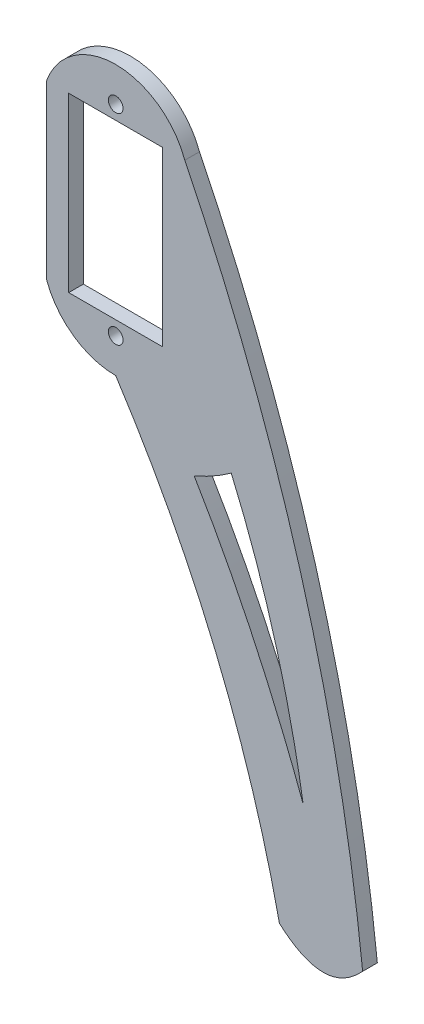
SolidWorks part; units mm, degrees
ref_plane "Front Plane" through (0, 0, 0) normal (0, 0, 1) x (1, 0, 0)
ref_plane "Top Plane" through (0, 0, 0) normal (0, 1, 0) x (1, 0, 0)
ref_plane "Right Plane" through (0, 0, 0) normal (1, 0, 0) x (0, 0, -1)
sketch "Sketch1" plane through (0, 0, 0) normal (0, 0, 1) x (1, 0, 0)
  line L0 (0, 11.75) -> (0, -11.75) construction
  line L1 (6.4, -11.75) -> (-6.4, -11.75)
  line L2 (6.4, -11.75) -> (6.4, 11.75)
  line L3 (6.4, 11.75) -> (-6.4, 11.75)
  line L4 (-6.4, -11.75) -> (-6.4, 11.75)
  line L5 (6.4, -11.75) -> (-6.4, 11.75) construction
  line L6 (6.4, 11.75) -> (-6.4, -11.75) construction
  line L9 (9.4, 11.75) -> (9.4, -11.75) construction
  line L10 (-9.4, 11.75) -> (-9.4, -11.75) construction
  line L11 (-6.4, -11.75) -> (6.4, -11.75)
  line L12 (-6.4, -11.75) -> (-6.4, -16.45) construction
  line L13 (6.4, -11.75) -> (6.4, -16.45) construction
  line L14 (-6.4, -16.45) -> (6.4, -16.45) construction
  line L15 (-38.4786, 0) -> (38.4786, 0) construction
  line L16 (-6.4, 16.45) -> (6.4, 16.45) construction
  line L17 (6.4, 11.75) -> (6.4, 16.45) construction
  line L18 (-6.4, 11.75) -> (-6.4, 16.45) construction
  line L19 (-9.4, -11.75) -> (-9.4, 11.75)
  line L20 (9.4, -11.75) -> (9.4, 11.75)
  line L21 (33.608, -71.75) -> (28.5034, -77.3391) construction
  line L22 (28.5034, -77.3391) -> (22.2808, -71.75) construction
  line L23 (15.7257, -21.9692) -> (22.5216, -37.7122) construction
  line L24 (22.5216, -37.7122) -> (25.5114, -56.0772) construction
  line L25 (10.6799, -24.817) -> (19.0882, -38.8473) construction
  line L26 (19.0882, -38.8473) -> (25.5114, -56.0772) construction
  arc A2 (9.4, 11.75) -> (-9.4, 11.75) centre (0, 11.75) ccw construction
  arc A3 (-9.4, -11.75) -> (9.4, -11.75) centre (0, -11.75) ccw construction
  circle A4 centre (0, -13.65) radius 1
  circle A5 centre (0, 13.65) radius 1
  arc A6 (-9.4, 11.75) -> (9.4, 11.75) centre (0, 8.3383) cw
  arc A7 (-9.4, -11.75) -> (9.4, -11.75) centre (0, -8.3383) ccw
  arc A8 (9.4, 11.75) -> (33.608, -71.75) centre (-214.9512, -98.5521) cw
  arc A9 (0, -18.3383) -> (22.2808, -71.75) centre (-134.0915, -105.6278) cw
  arc A10 (10.6799, -24.817) -> (15.7257, -21.9692) centre (0, 0) ccw
  spline S0 degree 2 poles (33.608, -71.75) (28.5034, -77.3391) (22.2808, -71.75) knots 0 0 0 1 1 1
  spline S1 degree 2 poles (15.7257, -21.9692) (22.5216, -37.7122) (25.5114, -56.0772) knots 0 0 0 1 1 1
  spline S2 degree 2 poles (10.6799, -24.817) (19.0882, -38.8473) (25.5114, -56.0772) knots 0 0 0 1 1 1
  point P0 (0, 0)
  point P8 (0, 0)
  point P18 (0, 0)
  point P20 (0, -16.45)
  dimension "D4" = 2
  dimension "D7" = 10
  dimension "D9" = 250
  dimension "D10" = 160
  dimension "D15" = 27.0175
  dimension "D1" = 12.8
  dimension "D2" = 23.5
  dimension "D3" = 4.7
  dimension "D5" = 2.8
  dimension "D6" = 3
  dimension "D8" = 60
  dimension "D11" = 22.2808
  dimension "D12" = 33.608
  dimension "D13" = 28.5034
  dimension "D14" = 77.3391
  dimension "D16" = 10.6799
  dimension "D17" = 15.7257
  dimension "D18" = 19.0882
  dimension "D19" = 22.5216
  dimension "D20" = 25.5114
  dimension "D21" = 37.7122
  dimension "D22" = 38.8473
  dimension "D23" = 56.0772
extrude "Boss-Extrude1" add sketch "Sketch1" along normal blind 2 contours L19 A7 L20 A6 A5 A4 L1 L4 L3 L2 | S0 A8 L20 A7 A9
